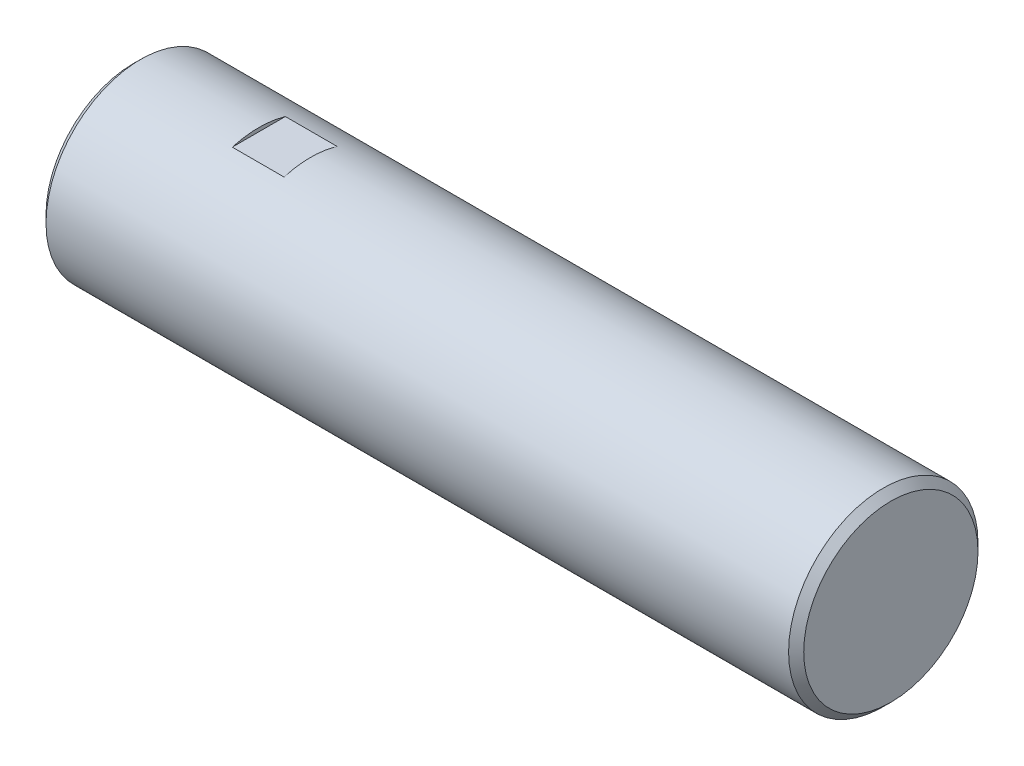
SolidWorks part; units mm, degrees
material "6061 Alloy"
ref_plane "Front Plane" through (0, 0, 0) normal (0, 0, 1) x (1, 0, 0)
ref_plane "Top Plane" through (0, 0, 0) normal (0, 1, 0) x (1, 0, 0)
ref_plane "Right Plane" through (0, 0, 0) normal (1, 0, 0) x (0, 0, -1)
sketch "Sketch2" plane through (0, 0, 0) normal (1, 0, 0) x (0, 0, -1)
  circle A0 centre (0, 0) radius 3.175
  dimension "D1" = 6.35
extrude "Boss-Extrude1" add sketch "Sketch2" along normal blind 25.4
chamfer "Chamfer1" distance 0.254 angle 45 2 edges at (25.4, 0, -3.175) (0, 0, -3.175)
sketch "Sketch3" plane through (0, 0, 0) normal (0, 0, 1) x (1, 0, 0)
  line L0 (25.146, 3.175) -> (0.254, 3.175) construction
  line L1 (4.2131, 6.304) -> (5.9469, 6.304)
  line L2 (4.2131, 6.304) -> (4.2131, 3.048)
  line L3 (4.2131, 3.048) -> (5.9469, 3.048)
  line L4 (5.9469, 6.304) -> (5.9469, 3.048)
  line L5 (4.2131, 6.304) -> (5.9469, 3.048) construction
  line L6 (4.2131, 3.048) -> (5.9469, 6.304) construction
  point P0 (5.08, 4.676)
  dimension "D1" = 5.08
  dimension "D2" = 0.127
extrude "Cut-Extrude1" cut sketch "Sketch3" against normal through all both and the other way through all
